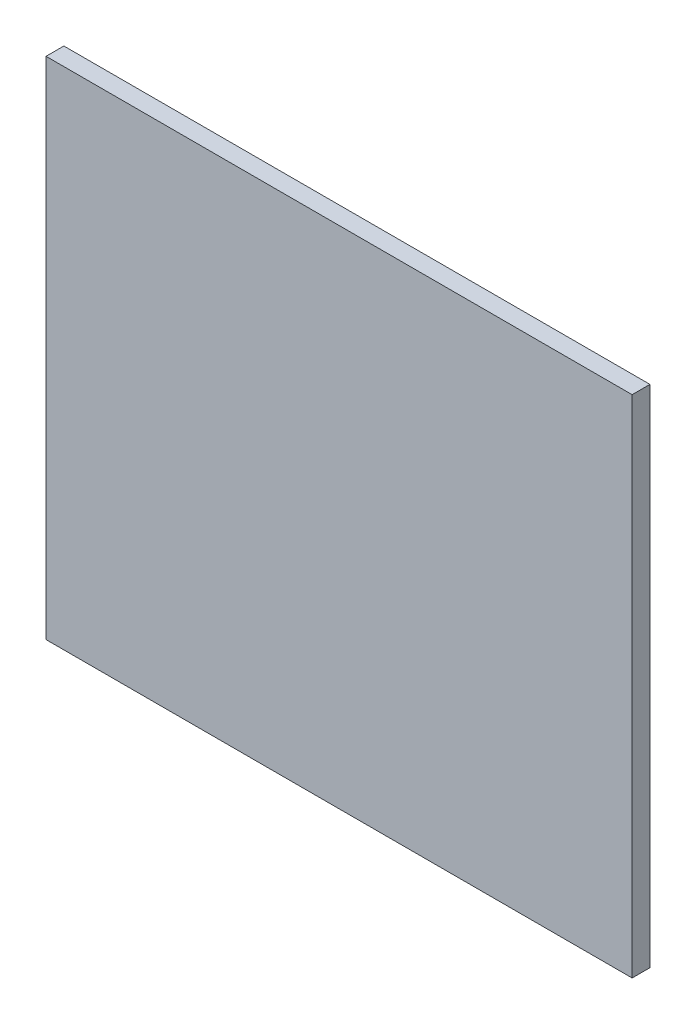
SolidWorks part; units mm, degrees
material "Vidro"
ref_plane "Plano frontal" through (0, 0, 0) normal (0, 0, 1) x (1, 0, 0)
ref_plane "Plano superior" through (0, 0, 0) normal (0, 1, 0) x (1, 0, 0)
ref_plane "Plano direito" through (0, 0, 0) normal (1, 0, 0) x (0, 0, -1)
sketch "Esboço1" plane through (0, 0, 0) normal (0, 0, 1) x (1, 0, 0)
  line L1 (-52.2063, -45) -> (52.2063, -45)
  line L2 (-52.2063, -45) -> (-52.2063, 45)
  line L3 (-52.2063, 45) -> (52.2063, 45)
  line L4 (52.2063, -45) -> (52.2063, 45)
  point P4 (52.2063, 0)
  point P7 (0, 45)
  dimension "D1" = 90
  dimension "D2" = 104.4125
extrude "Ressalto-extrusão1" add sketch "Esboço1" along normal blind 3.175
